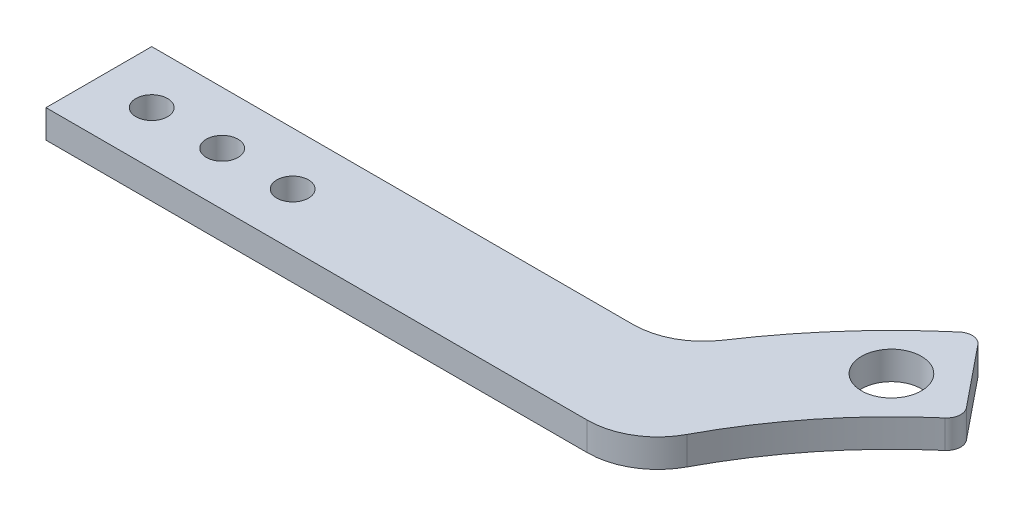
SolidWorks part; units mm, degrees
ref_plane "Front Plane" through (0, 0, 0) normal (0, 0, 1) x (1, 0, 0)
ref_plane "Top Plane" through (0, 0, 0) normal (0, 1, 0) x (1, 0, 0)
ref_plane "Right Plane" through (0, 0, 0) normal (1, 0, 0) x (0, 0, -1)
sketch "Sketch1" plane through (0, 0, 0) normal (0, 1, 0) x (1, 0, 0)
  circle A0 centre (0, 0) radius 77.5 construction
  circle A2 centre (0, 0) radius 85
  dimension "D1" = 155
  dimension "D2" = 170
extrude "Boss-Extrude1" add sketch "Sketch1" along normal blind 4
sketch "Sketch2" plane through (0, 4, 0) normal (0, 1, 0) x (1, 0, 0)
  line L0 (0, 0) -> (-85, 0) construction
  line L1 (0, 0) -> (-54.8008, 54.8008) construction
  circle A0 centre (0, 0) radius 85 construction
  circle A1 centre (0, 0) radius 77.5 construction
  circle A2 centre (-54.8008, 54.8008) radius 4.25
  dimension "D1" = 155
  dimension "D3" = 8.5
  dimension "D2" = 45
extrude "Cut-Extrude1" cut sketch "Sketch2" against normal through all
sketch "Sketch3" plane through (0, 4, 0) normal (0, 1, 0) x (1, 0, 0)
  line L0 (0, 0) -> (-85, 0)
  line L1 (0, 0) -> (-53.4922, 66.0574)
  line L2 (0, 0) -> (-54.8008, 54.8008) construction
  circle A0 centre (0, 0) radius 85 construction
  arc A1 (-85, 0) -> (-53.4922, 66.0574) centre (0, 0) ccw
  dimension "D1" = 6
extrude "Cut-Extrude2" cut sketch "Sketch3" against normal through all
sketch "Sketch5" plane through (0, 0, 0) normal (0, 1, 0) x (1, 0, 0)
  line L0 (0, 0) -> (-74.5013, 0) construction
  line L1 (-95.5916, -35) -> (-53.4111, -35)
  line L2 (-95.5916, -35) -> (-95.5916, 35)
  line L3 (-53.4111, -35) -> (-53.4111, 35)
  line L4 (-95.5916, 35) -> (-53.4111, 35)
  line L5 (-53.4111, 0) -> (-95.5916, 0) construction
  line L6 (-74.5013, -35) -> (-74.5013, 35) construction
  dimension "D1" = 70
extrude "Cut-Extrude4" cut sketch "Sketch5" along normal through all
sketch "Sketch6" plane through (0, 0, 0) normal (0, 1, 0) x (1, 0, 0)
  line L0 (-40.7322, 35) -> (-94.0959, 35) construction
  line L1 (-147.4597, 42.5) -> (-40.7322, 42.5)
  line L2 (-147.4597, 42.5) -> (-147.4597, 27.5)
  line L3 (-40.7322, 42.5) -> (-40.7322, 27.5)
  line L4 (-147.4597, 27.5) -> (-40.7322, 27.5)
  line L5 (-40.7322, 35) -> (-147.4597, 35) construction
  line L6 (-94.0959, 42.5) -> (-94.0959, 27.5) construction
  point P4 (-77.4597, 35)
  dimension "D1" = 15
  dimension "D2" = 70
extrude "Boss-Extrude3" add sketch "Sketch6" along normal blind 4
sketch "Sketch7" plane through (0, 0, 0) normal (0, 1, 0) x (1, 0, 0)
  circle A0 centre (0, 0) radius 70
  dimension "D1" = 140
extrude "Cut-Extrude5" cut sketch "Sketch7" along normal through all
sketch "Sketch8" plane through (0, 4, 0) normal (0, 1, 0) x (1, 0, 0)
  line L0 (-147.4597, 35) -> (-73.467, 35) construction
  line L1 (-147.4597, 42.5) -> (-147.4597, 27.5) construction
  circle A0 centre (-139.9597, 35) radius 2.25
  dimension "D1" = 4.5
  dimension "D2" = 7.5
extrude "Cut-Extrude6" cut sketch "Sketch8" against normal through all
pattern_linear "LPattern1" count 3 spacing 10 along (1, 0, 0) of "Cut-Extrude6"
fillet "Fillet1" radius 10 2 edges at (-73.6122, 2, -42.5) (-64.372, 2, -27.5)
fillet "Fillet2" radius 2 2 edges at (-44.0524, 2, -54.4002) (-53.4922, 2, -66.0574)
